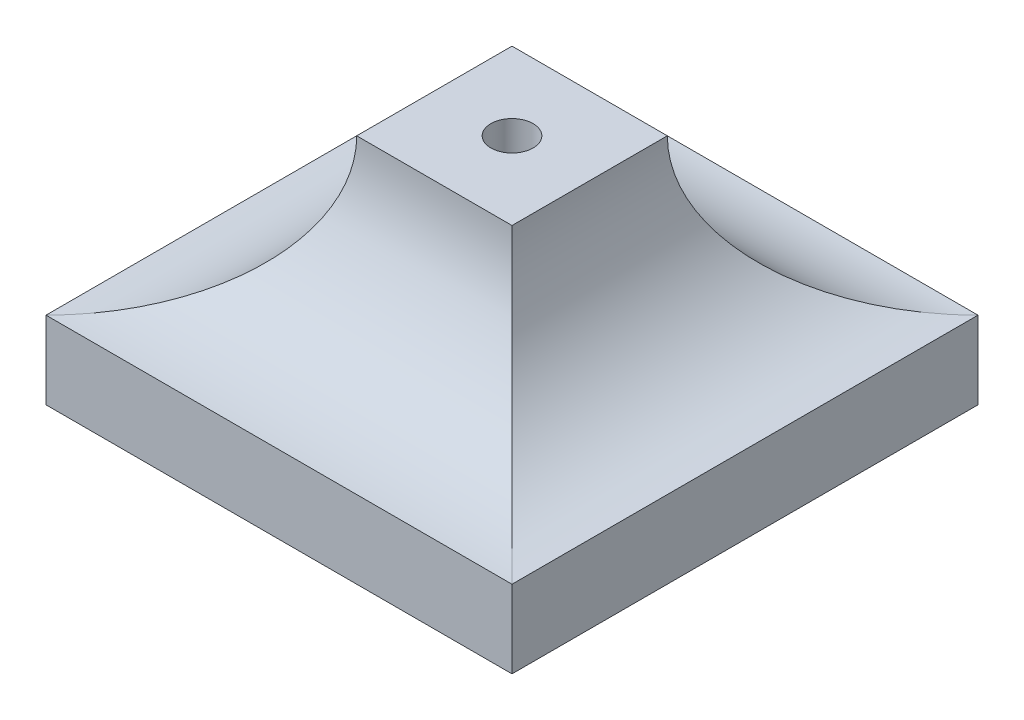
SolidWorks part; units mm, degrees
material "Onyx w/ CF"
ref_plane "Front Plane" through (0, 0, 0) normal (0, 0, 1) x (1, 0, 0)
ref_plane "Top Plane" through (0, 0, 0) normal (0, 1, 0) x (1, 0, 0)
ref_plane "Right Plane" through (0, 0, 0) normal (1, 0, 0) x (0, 0, -1)
sketch "Sketch1" plane through (0, 0, 0) normal (0, 1, 0) x (1, 0, 0)
  line L1 (-19.05, 19.05) -> (19.05, 19.05)
  line L2 (-19.05, 19.05) -> (-19.05, -19.05)
  line L3 (-19.05, -19.05) -> (19.05, -19.05)
  line L4 (19.05, 19.05) -> (19.05, -19.05)
  line L5 (-19.05, 19.05) -> (19.05, -19.05) construction
  line L6 (-19.05, -19.05) -> (19.05, 19.05) construction
  point P0 (0, 0)
  dimension "D1" = 38.1
extrude "Boss-Extrude1" add sketch "Sketch1" along normal blind 6.35
sketch "Sketch2" plane through (0, 0, 19.05) normal (0, 0, 1) x (1, 0, 0)
  line L0 (-19.05, 6.35) -> (19.05, 6.35)
  line L1 (-6.35, 19.05) -> (6.35, 19.05)
  arc A0 (-19.05, 6.35) -> (-6.35, 19.05) centre (-19.05, 19.05) ccw
  arc A1 (19.05, 6.35) -> (6.35, 19.05) centre (19.05, 19.05) cw
  dimension "D1" = 12.7
extrude "Boss-Extrude2" add sketch "Sketch2" against normal up to surface (38.1 mm away) up to face at (0, 3.175, -19.05)
sketch "Sketch3" plane through (19.05, 0, 0) normal (1, 0, 0) x (0, 0, -1)
  line L0 (-19.05, 6.35) -> (-19.05, 19.05)
  line L1 (-19.05, 19.05) -> (-6.35, 19.05)
  line L2 (0, 0) -> (0, 19.05) construction
  line L3 (-19.05, 0) -> (19.05, 0) construction
  line L4 (19.05, 6.35) -> (19.05, 19.05)
  line L5 (19.05, 19.05) -> (6.35, 19.05)
  arc A0 (-19.05, 6.35) -> (-6.35, 19.05) centre (-19.05, 19.05) ccw
  arc A1 (19.05, 6.35) -> (6.35, 19.05) centre (19.05, 19.05) cw
extrude "Cut-Extrude1" cut sketch "Sketch3" against normal through all
hole_wizard "#4 Clearance Hole1" positions "Sketch4" profile "Sketch5" hole size "#4" standard "ANSI Inch" end condition through all
sketch "Sketch4" plane through (0, 19.05, 0) normal (0, 1, 0) x (1, 0, 0)
  point P0 (0, 0)
sketch "Sketch5" plane through (0, 19.05, 0) normal (1, 0, 0) x (0, 0, 1)
  line L0 (0, 0) -> (0, 19.05)
  line L1 (0, 19.05) -> (1.7272, 19.05)
  line L2 (1.7272, 19.05) -> (1.7272, 0)
  line L5 (1.7272, 0) -> (0, 0)
  line L11 (0, -6.35) -> (0, 107.95) construction
  dimension "Thru Hole Dia." = 3.4544
  dimension "Thru Hole Depth" = 19.05
sketch "Sketch6" plane through (0, 0, 0) normal (0, -1, 0) x (1, 0, 0)
  circle A0 centre (0, 0) radius 3.9688
  dimension "D1" = 7.9375
extrude "Cut-Extrude2" cut sketch "Sketch6" against normal blind 6.35
